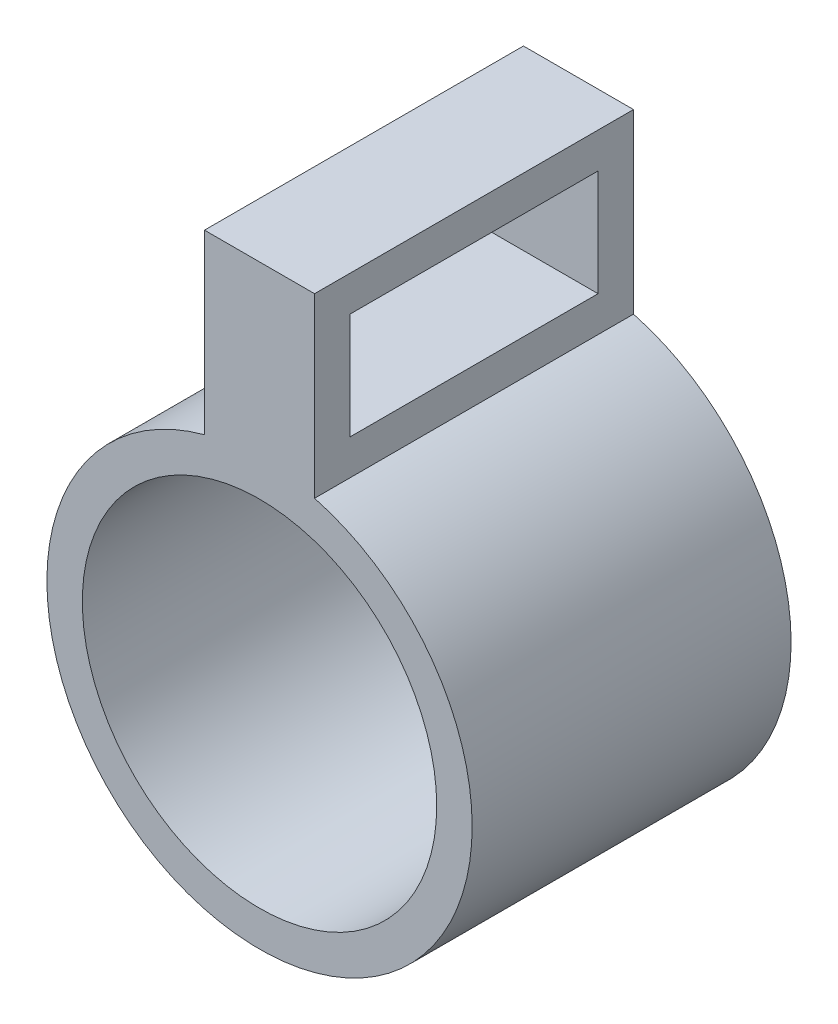
SolidWorks part; units mm, degrees
ref_plane "Ön Düzlem" through (0, 0, 0) normal (1, 0, 0) x (0, 1, 0)
ref_plane "Üst Düzlem" through (0, 0, 0) normal (0, 0, 1) x (0, 1, 0)
ref_plane "Sağ Düzlem" through (0, 0, 0) normal (0, 1, 0) x (-1, 0, 0)
sketch "Sketch1" plane through (0, 0, 0) normal (0, 0, 1) x (0, 1, 0)
  line L2 (0, 0) -> (-20.9005, 0) construction
  line L9 (11.5911, 3.1058) -> (21.5911, 3.1058)
  line L11 (11.5911, -3.1058) -> (21.5911, -3.1058)
  line L12 (21.5911, 3.1058) -> (21.5911, -3.1058)
  circle A0 centre (0, 0) radius 10
  arc A1 (11.5911, 3.1058) -> (11.5911, -3.1058) centre (0, 0) ccw
  circle A2 centre (0, 0) radius 12 construction
  dimension "D1" = 20
  dimension "D3" = 10
  dimension "D2" = 2
extrude "Boss-Extrude1" add sketch "Sketch1" along normal blind 16
sketch "Sketch2" plane through (0, 0, 0) normal (0, 0, -1) x (1, 0, 0)
  line L6 (-3.1058, -21.5911) -> (3.1058, -21.5911)
  line L7 (3.1058, -21.5911) -> (3.1058, -11.5911)
  line L8 (-3.1058, -11.5911) -> (-3.1058, -21.5911)
  line L9 (-3.1058, -21.5911) -> (3.1058, -21.5911)
  line L10 (3.1058, -21.5911) -> (3.1058, -11.5911)
  line L11 (-3.1058, -11.5911) -> (-3.1058, -21.5911)
  arc A3 (3.1058, -11.5911) -> (-3.1058, -11.5911) centre (0, 0) ccw
  arc A4 (3.1058, -11.5911) -> (-3.1058, -11.5911) centre (0, 0) ccw
  dimension "D1" = 0
extrude "Boss-Extrude2" add sketch "Sketch2" along normal blind 2
sketch "Sketch3" plane through (3.1058, 0, 0) normal (1, 0, 0) x (0, 1, 0)
  line L8 (13.5911, 14) -> (13.5911, 0)
  line L9 (13.5911, 0) -> (19.5911, 0)
  line L10 (19.5911, 0) -> (19.5911, 14)
  line L11 (19.5911, 14) -> (13.5911, 14)
  line L12 (13.5911, 14) -> (13.5911, 0)
  line L13 (13.5911, 0) -> (19.5911, 0)
  line L14 (19.5911, 0) -> (19.5911, 14)
  line L15 (19.5911, 14) -> (13.5911, 14)
  dimension "D1" = 2
extrude "Cut-Extrude1" cut sketch "Sketch3" against normal up to surface (6.2117 mm away) up to face at (-3.1058, 16.5911, 7)
